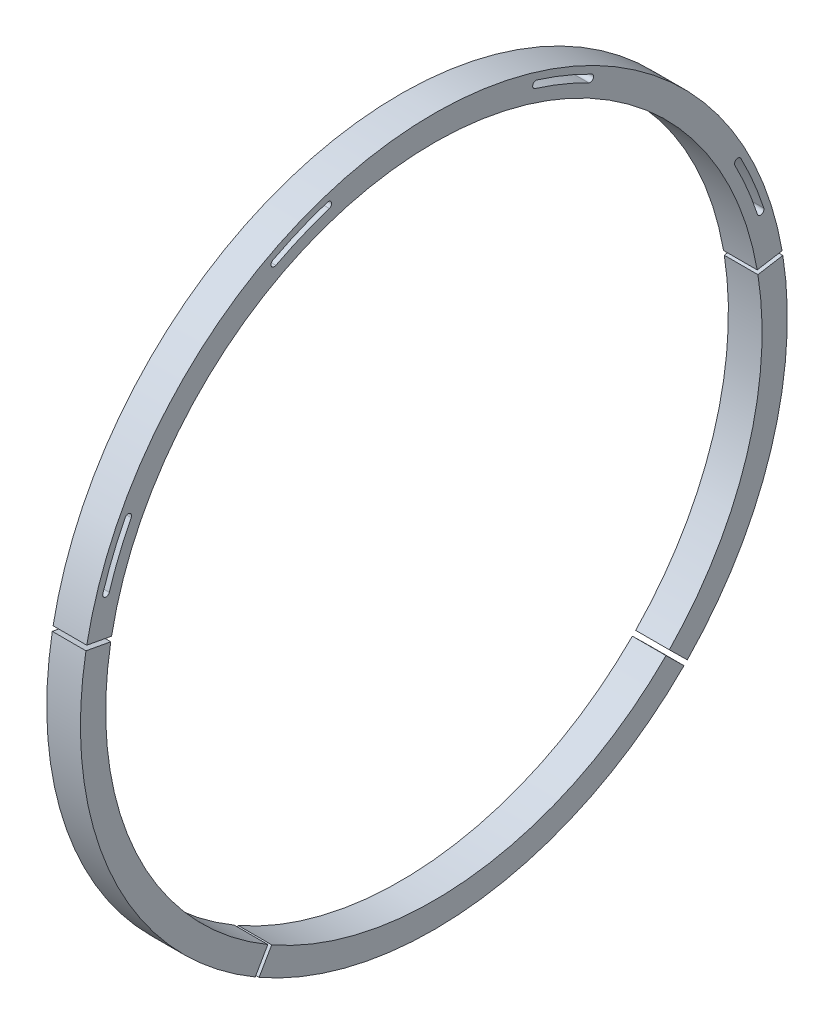
SolidWorks part; units mm, degrees
ref_plane "Front Plane" through (0, 0, 0) normal (0, 0, 1) x (1, 0, 0)
ref_plane "Top Plane" through (0, 0, 0) normal (0, 1, 0) x (1, 0, 0)
ref_plane "Right Plane" through (0, 0, 0) normal (1, 0, 0) x (0, 0, -1)
sketch "Sketch1" plane through (0, 0, 0) normal (1, 0, 0) x (0, 0, -1)
  line L0 (377.1506, 0) -> (-377.1506, 0) construction
  line L1 (137.9307, -137.841) -> (148.6168, -148.3679)
  line L2 (192.5417, 30.866) -> (207.3313, 33.3727)
  line L3 (139.8957, -135.8462) -> (150.5818, -146.3732)
  line L7 (192.1007, 33.501) -> (206.9007, 35.946)
  line L13 (-96.3409, -169.5389) -> (-103.8389, -182.5307)
  line L18 (-98.6546, -168.2031) -> (-106.1277, -181.2096)
  line L26 (-191.9736, 34.2216) -> (-206.7232, 36.9529)
  line L27 (-191.4868, 36.8485) -> (-206.2355, 39.5845)
  arc A0 (206.9007, 35.946) -> (-206.2355, 39.5845) centre (0, 0) ccw
  arc A1 (192.1007, 33.501) -> (-191.4868, 36.8485) centre (0, 0) ccw
  arc A2 (-103.8389, -182.5307) -> (136.0078, -160.0059) centre (0, 0) ccw
  arc A3 (-96.3409, -169.5389) -> (126.3639, -148.5165) centre (0, 0) ccw
  arc A4 (136.0078, -160.0059) -> (148.6168, -148.3679) centre (0, 0) ccw
  arc A5 (126.3639, -148.5165) -> (137.9307, -137.841) centre (0, 0) ccw
  arc A6 (-191.9736, 34.2216) -> (-98.6546, -168.2031) centre (0, 0) ccw
  arc A7 (-206.7232, 36.9529) -> (-106.1277, -181.2096) centre (0, 0) ccw
  arc A8 (139.8957, -135.8462) -> (192.5417, 30.866) centre (0, 0) ccw
  arc A9 (150.5818, -146.3732) -> (207.3313, 33.3727) centre (0, 0) ccw
  point P6 (0, 0)
  dimension "D1" = 195
  dimension "D2" = 195
  dimension "D5" = 210
  dimension "D6" = 210
  dimension "D10" = 2.6716
extrude "Boss-Extrude1" add sketch "Sketch1" along normal blind 20
ref_plane "Plane1" through (30, 0, 0) normal (1, 0, 0) x (0, 0, -1)
sketch "Sketch6" plane through (30, 0, 0) normal (1, 0, 0) x (0, 0, -1)
  line L1 (0, 0) -> (-309.8905, 0) construction
  line L2 (-195.3181, 58.7778) -> (-195.3557, 58.7891) construction
  arc A0 (196.0216, 63.3366) -> (182.4078, 95.7256) centre (0, 0) ccw
  arc A1 (192.2154, 62.1068) -> (178.8659, 93.8669) centre (0, 0) ccw
  arc A8 (-183.394, 93.8224) -> (-196.67, 61.2936) centre (0, 0) ccw
  arc A9 (-179.8329, 92.0006) -> (-192.8512, 60.1034) centre (0, 0) ccw
  arc A10 (-179.8329, 92.0006) -> (-183.394, 93.8224) centre (-181.6135, 92.9115) ccw
  arc A11 (-196.67, 61.2936) -> (-192.8512, 60.1034) centre (-194.7606, 60.6985) ccw
  arc A12 (-63.3366, 196.0216) -> (-95.7256, 182.4078) centre (0, 0) ccw
  arc A13 (-62.1068, 192.2154) -> (-93.8669, 178.8659) centre (0, 0) ccw
  arc A14 (-62.1068, 192.2154) -> (-63.3366, 196.0216) centre (-62.7217, 194.1185) ccw
  arc A15 (-95.7256, 182.4078) -> (-93.8669, 178.8659) centre (-94.7962, 180.6369) ccw
  arc A17 (93.8224, 183.394) -> (61.2936, 196.67) centre (0, 0) ccw
  arc A18 (92.0006, 179.8329) -> (60.1034, 192.8512) centre (0, 0) ccw
  arc A19 (92.0006, 179.8329) -> (93.8224, 183.394) centre (92.9115, 181.6135) ccw
  arc A20 (61.2936, 196.67) -> (60.1034, 192.8512) centre (60.6985, 194.7606) ccw
  arc A22 (196.0216, 63.3366) -> (182.4078, 95.7256) centre (0, 0) ccw
  arc A23 (192.2154, 62.1068) -> (178.8659, 93.8669) centre (0, 0) ccw
  arc A24 (192.2154, 62.1068) -> (196.0216, 63.3366) centre (194.1185, 62.7217) ccw
  arc A25 (182.4078, 95.7256) -> (178.8659, 93.8669) centre (180.6369, 94.7962) ccw
  arc A26 (-179.8329, 92.0006) -> (-192.8512, 60.1034) centre (0, 0) ccw
  arc A31 (-183.394, 93.8224) -> (-196.67, 61.2936) centre (0, 0) ccw
  arc A36 (-62.1068, 192.2154) -> (-93.8669, 178.8659) centre (0, 0) ccw
  arc A41 (-63.3366, 196.0216) -> (-95.7256, 182.4078) centre (0, 0) ccw
  arc A46 (92.0006, 179.8329) -> (60.1034, 192.8512) centre (0, 0) ccw
  arc A47 (93.8224, 183.394) -> (61.2936, 196.67) centre (0, 0) ccw
  point P12 (-195.3557, 58.7891)
  point P15 (-195.2836, 58.7674)
  point P19 (-188.875, 77.0858)
  point P25 (-79.0469, 188.0627)
  point P32 (77.0858, 188.875)
  point P67 (-188.0627, -79.0469)
  point P72 (0, 0)
extrude "Cut-Extrude1" cut sketch "Sketch6" against normal through all contours A8 A11 A9 A10 | A12 A15 A13 A14 | A17 A20 A18 A19 | A0 A25 A1 A24
